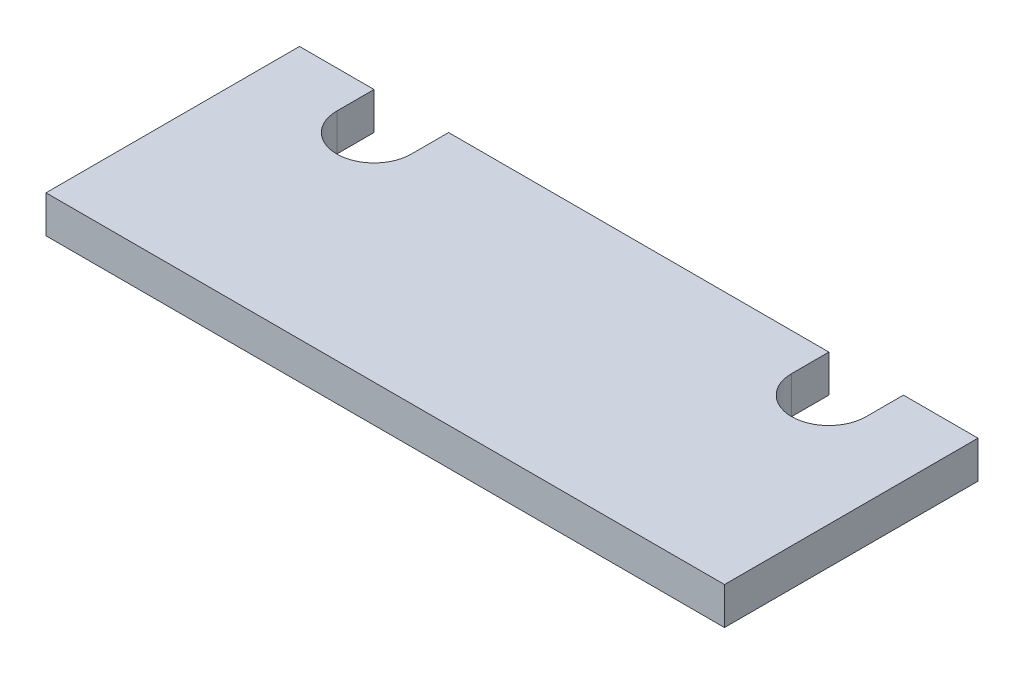
SolidWorks part; units mm, degrees
ref_plane "Front Plane" through (0, 0, 0) normal (0, 0, 1) x (1, 0, 0)
ref_plane "Top Plane" through (0, 0, 0) normal (0, 1, 0) x (1, 0, 0)
ref_plane "Right Plane" through (0, 0, 0) normal (1, 0, 0) x (0, 0, -1)
sketch "Sketch1" plane through (0, 0, 0) normal (0, 1, 0) x (1, 0, 0)
  line L1 (0, 0) -> (115.57, 0)
  line L2 (0, 0) -> (0, 43.18)
  line L3 (0, 43.18) -> (115.57, 43.18)
  line L4 (115.57, 0) -> (115.57, 43.18)
  dimension "D1" = 43.18
  dimension "D2" = 115.57
extrude "Boss-Extrude1" add sketch "Sketch1" along normal blind 6.35
sketch "Sketch2" plane through (0, 6.35, 0) normal (0, 1, 0) x (1, 0, 0)
  line L0 (19.05, 52.705) -> (19.05, 36.83) construction
  line L1 (115.57, 43.18) -> (0, 43.18) construction
  line L2 (25.4, 52.705) -> (25.4, 36.83)
  line L3 (12.7, 52.705) -> (12.7, 36.83)
  line L4 (12.7, 52.705) -> (25.4, 52.705)
  line L5 (57.785, 43.18) -> (57.785, 0) construction
  line L6 (0, 0) -> (115.57, 0) construction
  line L7 (0, 21.59) -> (115.57, 21.59) construction
  line L8 (0, 43.18) -> (0, 0) construction
  line L9 (115.57, 0) -> (115.57, 43.18) construction
  line L10 (115.57, 43.18) -> (0, 43.18) construction
  line L15 (96.52, 52.705) -> (96.52, 36.83) construction
  line L19 (102.87, 52.705) -> (90.17, 52.705)
  line L20 (102.87, 52.705) -> (102.87, 36.83)
  line L21 (90.17, 52.705) -> (90.17, 36.83)
  arc A1 (12.7, 36.83) -> (25.4, 36.83) centre (19.05, 36.83) ccw
  arc A2 (102.87, 36.83) -> (90.17, 36.83) centre (96.52, 36.83) cw
  point P4 (9.1229, 43.18)
  point P25 (9.1229, 0)
  point P39 (106.4471, 43.18)
  dimension "D1" = 6.35
  dimension "D2" = 6.35
  dimension "D3" = 12.7
extrude "Cut-Extrude1" cut sketch "Sketch2" against normal through all
